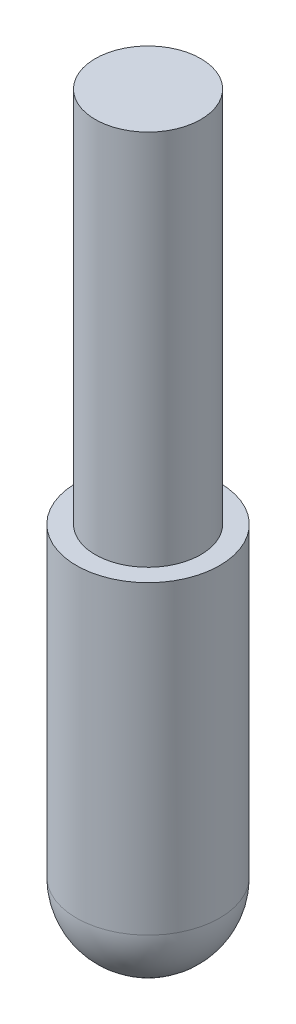
SolidWorks part; units mm, degrees
ref_plane "Front Plane" through (0, 0, 0) normal (0, 0, 1) x (1, 0, 0)
ref_plane "Top Plane" through (0, 0, 0) normal (0, 1, 0) x (1, 0, 0)
ref_plane "Right Plane" through (0, 0, 0) normal (1, 0, 0) x (0, 0, -1)
sketch "Sketch1" plane through (0, 0, 0) normal (1, 0, 0) x (0, 0, -1)
  line L0 (0, 25) -> (3.5, 25)
  line L1 (3.5, 25) -> (3.5, 0)
  line L2 (3.5, 0) -> (4.75, 0)
  line L3 (4.75, 0) -> (4.75, -20.25)
  line L5 (0, -25) -> (0, 25)
  arc A0 (0, -25) -> (4.75, -20.25) centre (0, -20.25) ccw
  dimension "D1" = 25
  dimension "D2" = 20.25
  dimension "D3" = 4.75
  dimension "D4" = 3.5
  dimension "D5" = 50
revolve "Revolve1" add sketch "Sketch1" angle 360 about L5
